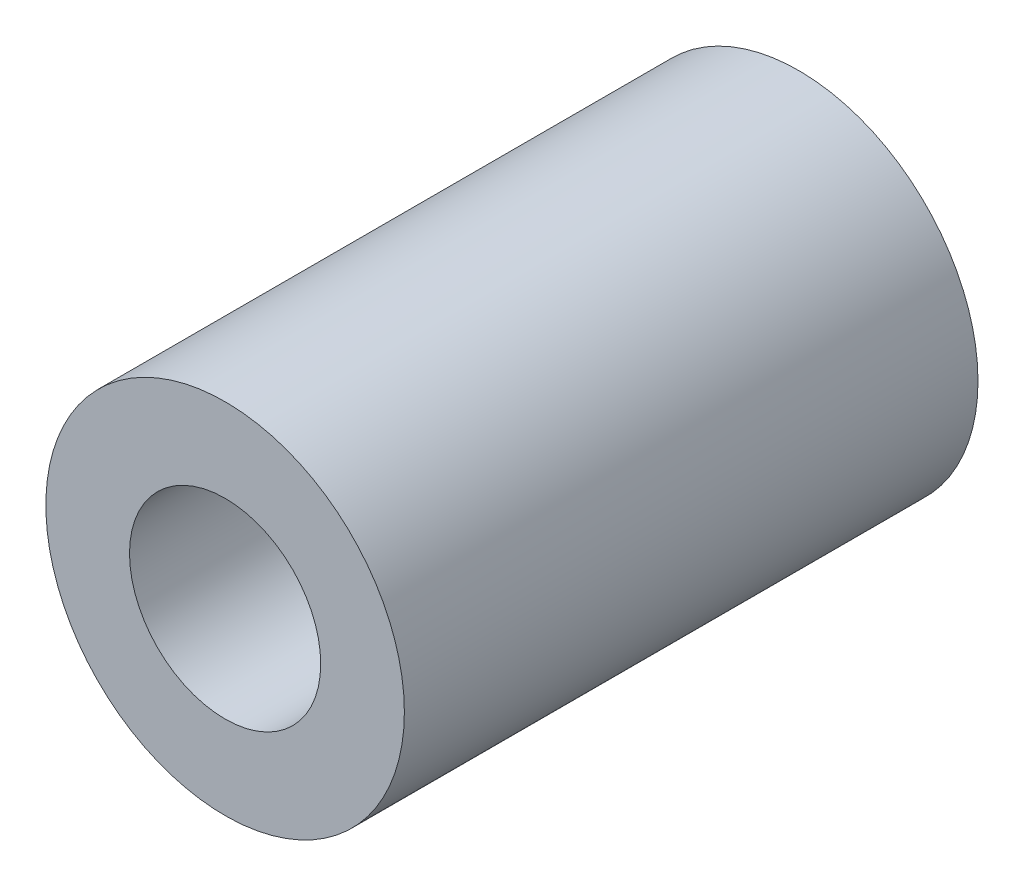
SolidWorks part; units mm, degrees
ref_plane "Plan de face" through (0, 0, 0) normal (0, 0, 1) x (1, 0, 0)
ref_plane "Plan de dessus" through (0, 0, 0) normal (0, 1, 0) x (1, 0, 0)
ref_plane "Plan de droite" through (0, 0, 0) normal (1, 0, 0) x (0, 0, -1)
sketch "Esquisse1" plane through (0, 0, 0) normal (0, 0, 1) x (1, 0, 0)
  circle A0 centre (0, 0) radius 4
  circle A1 centre (0, 0) radius 7.5
  dimension "D1" = 8
  dimension "D2" = 15
extrude "Boss.-Extru.1" add sketch "Esquisse1" along normal blind 24
